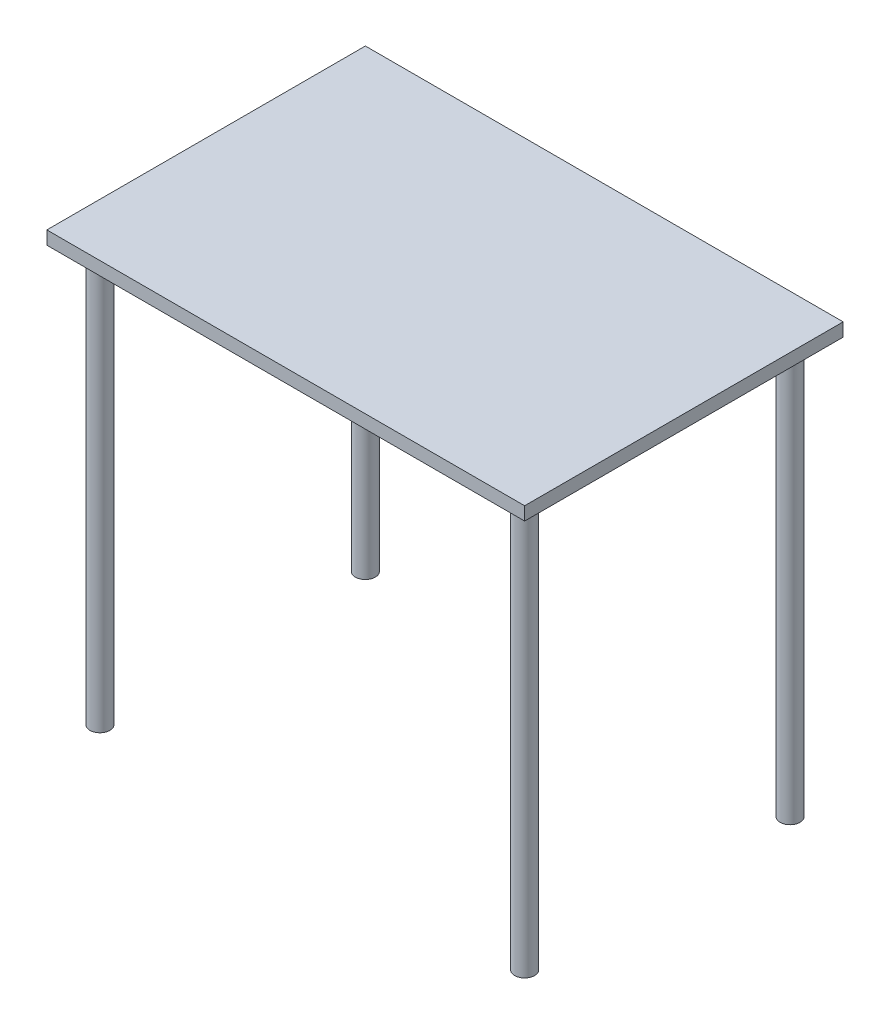
SolidWorks part; units mm, degrees
ref_plane "Front Plane" through (0, 0, 0) normal (0, 0, 1) x (1, 0, 0)
ref_plane "Top Plane" through (0, 0, 0) normal (0, 1, 0) x (1, 0, 0)
ref_plane "Right Plane" through (0, 0, 0) normal (1, 0, 0) x (0, 0, -1)
sketch "Sketch3" plane through (0, 0, 0) normal (0, 1, 0) x (1, 0, 0)
  line L1 (0, 0) -> (914.4, 0)
  line L2 (0, 0) -> (0, 609.6)
  line L3 (0, 609.6) -> (914.4, 609.6)
  line L4 (914.4, 0) -> (914.4, 609.6)
  dimension "D1" = 914.4
  dimension "D2" = 609.6
extrude "Table" add sketch "Sketch3" along normal blind 25.4
sketch "Sketch4" plane through (0, 0, 0) normal (0, -1, 0) x (1, 0, 0)
  line L0 (50.8, -50.8) -> (0, -50.8) construction
  line L1 (0, 0) -> (50.8, 0) construction
  line L2 (0, 0) -> (0, -50.8) construction
  line L4 (50.8, 0) -> (50.8, -50.8) construction
  line L5 (0, -609.6) -> (50.8, -609.6) construction
  line L6 (0, -609.6) -> (0, -558.8) construction
  line L7 (0, -558.8) -> (50.8, -558.8) construction
  line L8 (50.8, -609.6) -> (50.8, -558.8) construction
  line L9 (914.4, -609.6) -> (863.6, -609.6) construction
  line L10 (914.4, -609.6) -> (914.4, -558.8) construction
  line L11 (914.4, -558.8) -> (863.6, -558.8) construction
  line L12 (863.6, -609.6) -> (863.6, -558.8) construction
  line L13 (914.4, 0) -> (863.6, 0) construction
  line L14 (914.4, 0) -> (914.4, -50.8) construction
  line L15 (914.4, -50.8) -> (863.6, -50.8) construction
  line L16 (863.6, 0) -> (863.6, -50.8) construction
  circle A0 centre (50.8, -50.8) radius 19.05
  circle A1 centre (863.6, -50.8) radius 19.05
  circle A2 centre (50.8, -558.8) radius 19.05
  circle A3 centre (863.6, -558.8) radius 19.05
  dimension "D1" = 38.1
  dimension "D2" = 50.8
extrude "Legs" add sketch "Sketch4" along normal offset from surface (794.675 mm away) 820.075 up to face at (457.2, 25.4, -304.8)
sketch "Sketch5" plane through (0, 0, 0) normal (0, 0, 1) x (1, 0, 0)
  line L0 (0, 25.4) -> (0, -838.2) construction
  dimension "D1" = 863.6
